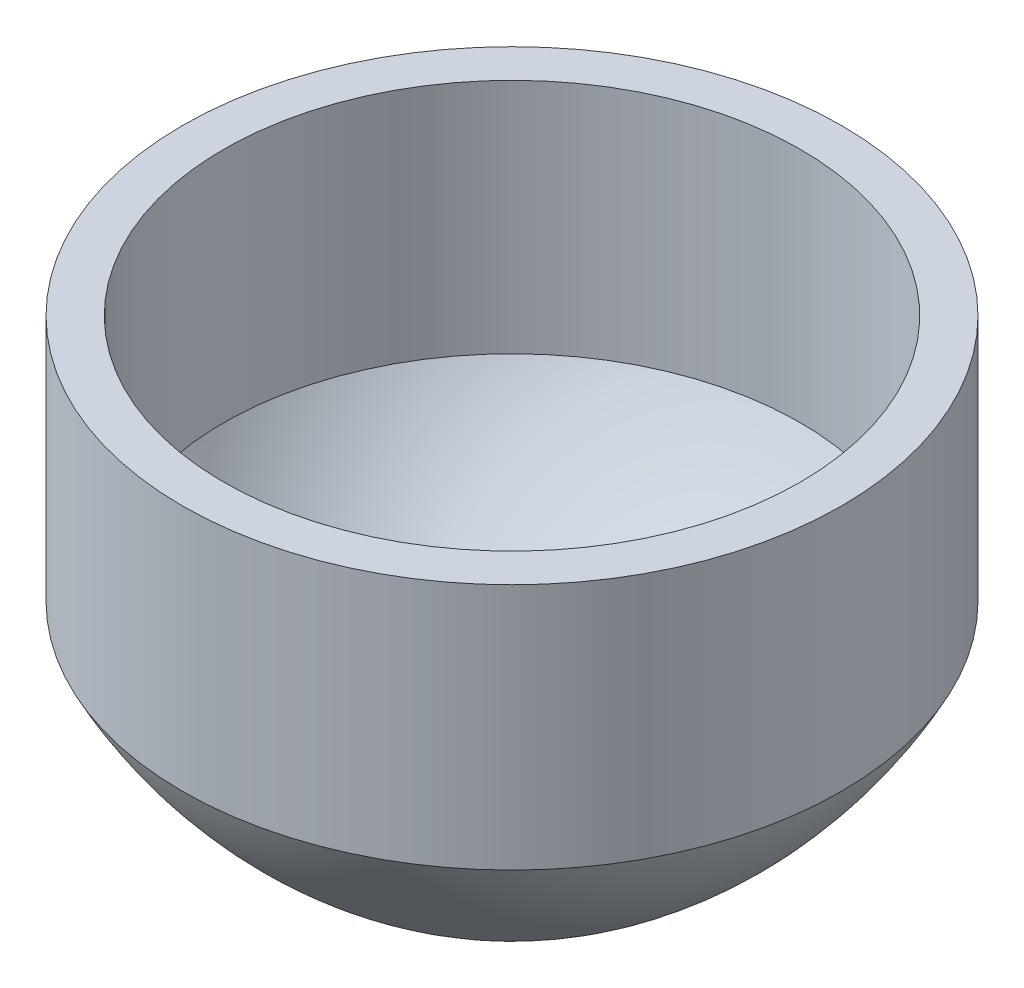
SolidWorks part; units mm, degrees
ref_plane "Front Plane" through (0, 0, 0) normal (0, 0, 1) x (1, 0, 0)
ref_plane "Top Plane" through (0, 0, 0) normal (0, 1, 0) x (1, 0, 0)
ref_plane "Right Plane" through (0, 0, 0) normal (1, 0, 0) x (0, 0, -1)
sketch "Sketch1" plane through (0, 0, 0) normal (0, 0, 1) x (1, 0, 0)
  line L0 (0, -1000) -> (0, 49000) construction
  line L1 (-1000, 0) -> (49000, 0) construction
  line L2 (1400, 0) -> (1600, 0)
  line L3 (1600, 0) -> (1600, -1200)
  line L4 (0, -2154.1554) -> (0, -2357.0336)
  line L5 (1400, 0) -> (1400, -1149.8899)
  line L6 (1400, -170.8419) -> (1400, -1149.8899) construction
  line L8 (-183279.9493, 29051.3983) -> (1400, -170.8419) construction
  line L9 (0, -2154.1554) -> (-183279.9493, 29051.3983) construction
  line L10 (0, -2357.0336) -> (-216976.5473, 34585.7598) construction
  line L11 (-216976.5473, 34585.7598) -> (1600, 0) construction
  arc A0 (1600, -1200) -> (0, -2357.0336) centre (-352.0656, -185.3868) cw
  arc A1 (1400, -1149.8899) -> (0, -2154.1554) centre (-352.0656, -185.3868) cw
  dimension "D3" = 2357.0336
  dimension "D5" = 2000
  dimension "D1" = 3200
  dimension "D2" = 1200
  dimension "D4" = 200
revolve "Revolve1" add sketch "Sketch1" angle 360 about L0
